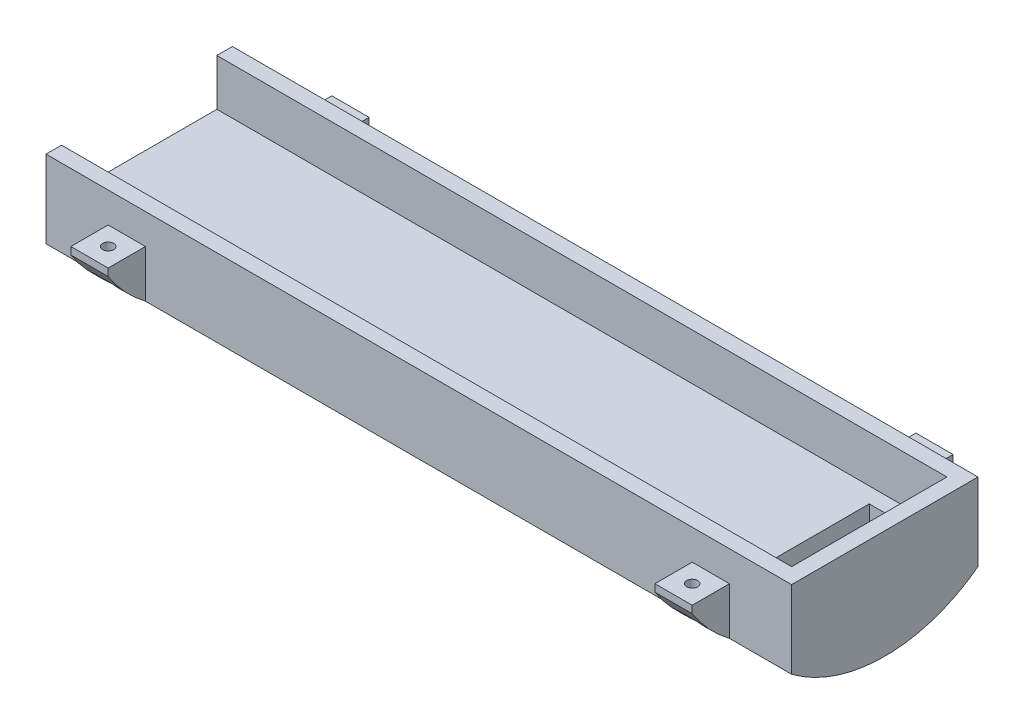
SolidWorks part; units mm, degrees
ref_plane "Front Plane" through (0, 0, 0) normal (0, 0, 1) x (1, 0, 0)
ref_plane "Top Plane" through (0, 0, 0) normal (0, 1, 0) x (1, 0, 0)
ref_plane "Right Plane" through (0, 0, 0) normal (1, 0, 0) x (0, 0, -1)
sketch "Sketch1" plane through (0, 0, 0) normal (0, 1, 0) x (1, 0, 0)
  line L1 (-152.4, -38.1) -> (152.4, -38.1)
  line L2 (-152.4, -38.1) -> (-152.4, 38.1)
  line L3 (-152.4, 38.1) -> (152.4, 38.1)
  line L4 (152.4, -38.1) -> (152.4, 38.1)
  line L5 (-152.4, -38.1) -> (152.4, 38.1) construction
  line L6 (-152.4, 38.1) -> (152.4, -38.1) construction
  point P0 (0, 0)
  dimension "D1" = 76.2
  dimension "D2" = 304.8
extrude "Boss-Extrude1" add sketch "Sketch1" against normal blind 6.35
sketch "Sketch3" plane through (0, 0, 0) normal (0, 1, 0) x (1, 0, 0)
  line L0 (152.4, -38.1) -> (152.4, 38.1) construction
  line L1 (120.65, -25.4) -> (146.05, -25.4)
  line L2 (120.65, -25.4) -> (120.65, 25.4)
  line L3 (120.65, 25.4) -> (146.05, 25.4)
  line L4 (146.05, -25.4) -> (146.05, 25.4)
  line L5 (120.65, -25.4) -> (146.05, 25.4) construction
  line L6 (120.65, 25.4) -> (146.05, -25.4) construction
  point P0 (133.35, 0)
  dimension "D1" = 25.4
  dimension "D2" = 50.8
  dimension "D3" = 6.35
extrude "Cut-Extrude2" cut sketch "Sketch3" against normal blind 25.4
sketch "Sketch4" plane through (0, 0, 0) normal (0, 1, 0) x (1, 0, 0)
  line L0 (152.4, -38.1) -> (152.4, 38.1) construction
  line L1 (-152.4, 38.1) -> (152.4, 38.1)
  line L2 (-152.4, 38.1) -> (-152.4, 31.75)
  line L3 (-152.4, 31.75) -> (152.4, 31.75)
  line L4 (152.4, 38.1) -> (152.4, 31.75)
  line L5 (146.05, -25.4) -> (146.05, 25.4) construction
  line L6 (-152.4, -38.1) -> (152.4, -38.1)
  line L7 (-152.4, -38.1) -> (-152.4, -31.75)
  line L8 (-152.4, -31.75) -> (152.4, -31.75)
  line L9 (152.4, -38.1) -> (152.4, -31.75)
  line L10 (152.4, 31.75) -> (146.05, 31.75)
  line L11 (152.4, 31.75) -> (152.4, -31.75)
  line L12 (152.4, -31.75) -> (146.05, -31.75)
  line L13 (146.05, 31.75) -> (146.05, -31.75)
  line M7 (146.05, 25.4) -> (146.05, -25.4)
  line M10 (152.4, -38.1) -> (152.4, 38.1)
  line M11 (152.4, 38.1) -> (-152.4, 38.1)
  line M12 (-152.4, 38.1) -> (-152.4, -38.1)
  line M13 (-152.4, -38.1) -> (152.4, -38.1)
  dimension "D1" = 6.35
  dimension "D2" = 6.35
extrude "Boss-Extrude2" add sketch "Sketch4" along normal blind 19.05 contours L3 M12 M10 M11 | L8 M12 M13 M10 | L3 L13 L8 M7 M10
sketch "Sketch5" plane through (-152.4, 0, 0) normal (-1, 0, 0) x (0, 0, 1)
  line L0 (-31.75, 19.05) -> (31.75, 19.05) construction
  line L1 (-38.1, -6.35) -> (-38.1, -12.7)
  line L2 (38.1, -6.35) -> (38.1, -12.7)
  line L3 (-38.1, -6.35) -> (38.1, -6.35)
  circle A0 centre (0, 38.1) radius 63.5
  line M5 (-38.1, -6.35) -> (38.1, -6.35)
  dimension "D1" = 127
  dimension "D2" = 19.05
extrude "Boss-Extrude3" add sketch "Sketch5" against normal up to surface (304.8 mm away) contours L1 A0 L2 M5
sketch "Sketch6" plane through (-152.4, 0, 0) normal (-1, 0, 0) x (0, 0, 1)
  line L0 (-53.34, 6.6675) -> (-38.1, 6.6675)
  line L1 (-38.1, -12.7) -> (-38.1, 19.05) construction
  line L2 (38.1, -10.7011) -> (38.1, -12.7)
  line L3 (53.34, 3.6458) -> (53.34, 6.6675)
  line L4 (38.1, -10.7011) -> (38.1, -12.7)
  line L5 (53.34, 3.6458) -> (53.34, 6.6675)
  line L6 (-53.34, 6.6675) -> (-53.34, 3.6458)
  line L7 (-38.1, -12.7) -> (-38.1, -10.7011)
  line L8 (-53.34, 6.6675) -> (-53.34, 3.6458)
  line L10 (53.34, 6.6675) -> (38.1, 6.6675)
  line L11 (38.1, -12.7) -> (38.1, 19.05) construction
  line L12 (-38.1, 6.6675) -> (-38.1, -10.7011)
  line L13 (38.1, 6.6675) -> (38.1, -10.7011)
  line L20 (-38.1, -12.7) -> (-38.1, -10.7011)
  arc A2 (38.1, -12.7) -> (53.34, 3.6458) centre (0, 38.1) ccw
  arc A3 (38.1, -10.7011) -> (53.34, 6.6675) centre (0, 38.1) ccw
  arc A4 (38.1, -12.7) -> (53.34, 3.6458) centre (0, 38.1) ccw
  arc A5 (38.1, -10.7011) -> (53.34, 6.6675) centre (0, 38.1) ccw
  arc A6 (-53.34, 6.6675) -> (-38.1, -10.7011) centre (0, 38.1) ccw
  arc A7 (-53.34, 3.6458) -> (-38.1, -12.7) centre (0, 38.1) ccw
  arc A8 (-53.34, 6.6675) -> (-38.1, -10.7011) centre (0, 38.1) ccw
  arc A9 (-53.34, 3.6458) -> (-38.1, -12.7) centre (0, 38.1) ccw
  dimension "D1" = 0
  dimension "D2" = 0
ref_plane "Plane1" through (-127, 0, 0) normal (-1, 0, 0) x (0, 0, 1)
ref_plane "Plane2" through (111.76, 0, 0) normal (-1, 0, 0) x (0, 0, 1)
sketch "Sketch8" plane through (-127, 0, 0) normal (-1, 0, 0) x (0, 0, 1)
  line L0 (-53.34, 6.6675) -> (-53.34, 3.6458) construction
  line L2 (-53.34, 6.6675) -> (-38.1, 6.6675) construction
  line L3 (-38.1, 6.6675) -> (-38.1, -10.7011) construction
  line L4 (38.1, -10.7011) -> (38.1, -12.7) construction
  line L5 (53.34, 3.6458) -> (53.34, 6.6675) construction
  line L6 (53.34, 6.6675) -> (38.1, 6.6675) construction
  line L7 (38.1, 6.6675) -> (38.1, -10.7011) construction
  line L8 (-53.34, 6.6675) -> (-53.34, 3.6458)
  line L10 (-53.34, 6.6675) -> (-38.1, 6.6675)
  line L11 (-38.1, 6.6675) -> (-38.1, -10.7011)
  line L12 (38.1, -10.7011) -> (38.1, -12.7)
  line L13 (53.34, 3.6458) -> (53.34, 6.6675)
  line L14 (53.34, 6.6675) -> (38.1, 6.6675)
  line L15 (38.1, 6.6675) -> (38.1, -10.7011)
  line L16 (-38.1, -10.7011) -> (-38.1, -12.7)
  arc A0 (-53.34, 3.6458) -> (-38.1, -12.7) centre (0, 38.1) ccw construction
  arc A1 (-53.34, 6.6675) -> (-38.1, -10.7011) centre (0, 38.1) ccw construction
  arc A2 (38.1, -12.7) -> (53.34, 3.6458) centre (0, 38.1) ccw construction
  arc A3 (38.1, -10.7011) -> (53.34, 6.6675) centre (0, 38.1) ccw construction
  arc A4 (-53.34, 3.6458) -> (-38.1, -12.7) centre (0, 38.1) ccw
  arc A5 (-53.34, 6.6675) -> (-38.1, -10.7011) centre (0, 38.1) ccw
  arc A6 (38.1, -12.7) -> (53.34, 3.6458) centre (0, 38.1) ccw
  arc A7 (38.1, -10.7011) -> (53.34, 6.6675) centre (0, 38.1) ccw
extrude "Boss-Extrude4" add sketch "Sketch8" against normal blind 15.24
sketch "Sketch9" plane through (111.76, 0, 0) normal (-1, 0, 0) x (0, 0, 1)
  line L0 (-53.34, 6.6675) -> (-53.34, 3.6458) construction
  line L2 (-53.34, 6.6675) -> (-38.1, 6.6675) construction
  line L3 (-38.1, 6.6675) -> (-38.1, -10.7011) construction
  line L4 (38.1, -10.7011) -> (38.1, -12.7) construction
  line L5 (53.34, 3.6458) -> (53.34, 6.6675) construction
  line L6 (53.34, 6.6675) -> (38.1, 6.6675) construction
  line L7 (38.1, 6.6675) -> (38.1, -10.7011) construction
  line L8 (-53.34, 6.6675) -> (-53.34, 3.6458)
  line L10 (-53.34, 6.6675) -> (-38.1, 6.6675)
  line L11 (-38.1, 6.6675) -> (-38.1, -10.7011)
  line L12 (38.1, -10.7011) -> (38.1, -12.7)
  line L13 (53.34, 3.6458) -> (53.34, 6.6675)
  line L14 (53.34, 6.6675) -> (38.1, 6.6675)
  line L15 (38.1, 6.6675) -> (38.1, -10.7011)
  line L16 (-38.1, -10.7011) -> (-38.1, -12.7)
  arc A0 (-53.34, 3.6458) -> (-38.1, -12.7) centre (0, 38.1) ccw construction
  arc A1 (-53.34, 6.6675) -> (-38.1, -10.7011) centre (0, 38.1) ccw construction
  arc A2 (38.1, -12.7) -> (53.34, 3.6458) centre (0, 38.1) ccw construction
  arc A3 (38.1, -10.7011) -> (53.34, 6.6675) centre (0, 38.1) ccw construction
  arc A4 (-53.34, 3.6458) -> (-38.1, -12.7) centre (0, 38.1) ccw
  arc A5 (-53.34, 6.6675) -> (-38.1, -10.7011) centre (0, 38.1) ccw
  arc A6 (38.1, -12.7) -> (53.34, 3.6458) centre (0, 38.1) ccw
  arc A7 (38.1, -10.7011) -> (53.34, 6.6675) centre (0, 38.1) ccw
extrude "Boss-Extrude5" add sketch "Sketch9" against normal blind 15.24
ref_plane "Plane3" through (0, -6.0325, 0) normal (0, 1, 0) x (1, 0, 0)
sketch "Sketch10" plane through (0, -6.0325, 0) normal (0, 1, 0) x (1, 0, 0)
  line L0 (-127, 53.34) -> (-127, 38.1) construction
  line L1 (-111.76, 53.34) -> (-127, 53.34) construction
  line L2 (127, 53.34) -> (111.76, 53.34) construction
  line L3 (111.76, 53.34) -> (111.76, 38.1) construction
  line L4 (-24.4475, 0) -> (24.4475, 0) construction
  circle A0 centre (-119.38, 45.72) radius 2.54
  circle A1 centre (119.38, 45.72) radius 2.54
  circle A2 centre (119.38, -45.72) radius 2.54
  circle A3 centre (-119.38, -45.72) radius 2.54
  point P12 (119.3443, 44.9908)
  dimension "D1" = 5.08
  dimension "D4" = 5.08
  dimension "D2" = 7.62
  dimension "D3" = 7.62
  dimension "D5" = 7.62
  dimension "D6" = 7.62
hole_wizard "CBORE for #8 Binding Head Machine Screw1" positions "3DSketch1" profile "Sketch11" counterbore size "#8" standard "ANSI Inch"
sketch3d "3DSketch1"
  point P0 (-119.38, -6.0325, -45.72)
  point P3 (119.38, -6.0325, -45.72)
  point P6 (119.38, -6.0325, 45.72)
  point P9 (-119.38, -6.0325, 45.72)
sketch "Sketch11" plane through (-119.38, -6.0325, -45.72) normal (1, 0, 0) x (0, 0, -1)
  line L0 (0, 0) -> (0, 25.0825)
  line L1 (0, 25.0825) -> (2.2479, 25.0825)
  line L3 (2.2479, 25.0825) -> (2.2479, 2.667)
  line L4 (2.2479, 2.667) -> (4.7625, 2.667)
  line L5 (4.7625, 2.667) -> (4.7625, 0)
  line L7 (4.7625, 0) -> (0, 0)
  line L11 (0, -6.35) -> (0, 107.95) construction
  dimension "Thru Hole Dia." = 4.4958
  dimension "Thru Hole Depth" = 25.0825
  dimension "C'Bore Dia." = 9.525
  dimension "C'Bore Depth" = 2.667
sketch "Sketch12" plane through (0, -3.3655, 0) normal (0, -1, 0) x (1, 0, 0)
  line L0 (123.5096, 48.0922) -> (115.2504, 48.0922) construction
  line L1 (115.2504, -48.0922) -> (123.5096, -48.0922) construction
  line L2 (-123.5096, -48.0922) -> (-115.2504, -48.0922) construction
  line L3 (-115.2504, 48.0922) -> (-123.5096, 48.0922) construction
  line L4 (123.5096, 48.0922) -> (115.2504, 48.0922)
  line L5 (115.2504, -48.0922) -> (123.5096, -48.0922)
  line L6 (-123.5096, -48.0922) -> (-115.2504, -48.0922)
  line L7 (-115.2504, 48.0922) -> (-123.5096, 48.0922)
  arc A0 (115.2504, 48.0922) -> (123.5096, 48.0922) centre (119.38, 45.72) ccw construction
  arc A1 (123.5096, -48.0922) -> (115.2504, -48.0922) centre (119.38, -45.72) ccw construction
  arc A2 (-115.2504, -48.0922) -> (-123.5096, -48.0922) centre (-119.38, -45.72) ccw construction
  arc A3 (-123.5096, 48.0922) -> (-115.2504, 48.0922) centre (-119.38, 45.72) ccw construction
  arc A4 (115.2504, 48.0922) -> (123.5096, 48.0922) centre (119.38, 45.72) ccw
  arc A5 (123.5096, -48.0922) -> (115.2504, -48.0922) centre (119.38, -45.72) ccw
  arc A6 (-115.2504, -48.0922) -> (-123.5096, -48.0922) centre (-119.38, -45.72) ccw
  arc A7 (-123.5096, 48.0922) -> (-115.2504, 48.0922) centre (-119.38, 45.72) ccw
  circle A8 centre (-119.38, 45.72) radius 4.7625
  circle A9 centre (119.38, 45.72) radius 4.7625
  circle A10 centre (119.38, -45.72) radius 4.7625
  circle A11 centre (-119.38, -45.72) radius 4.7625
  line M1 (-115.2504, 48.0922) -> (-123.5096, 48.0922)
  arc M2 (-123.5096, 48.0922) -> (-115.2504, 48.0922) centre (-119.38, 45.72) ccw
  circle M3 centre (-119.38, 45.72) radius 2.2479
extrude "Cut-Extrude3" cut sketch "Sketch12" along normal through all contours L6 A6 | L6 A11 | A8 M1 | M2 M1 M3 | L4 A9 | L4 A4 | L5 A5 | L5 A10 | M3
